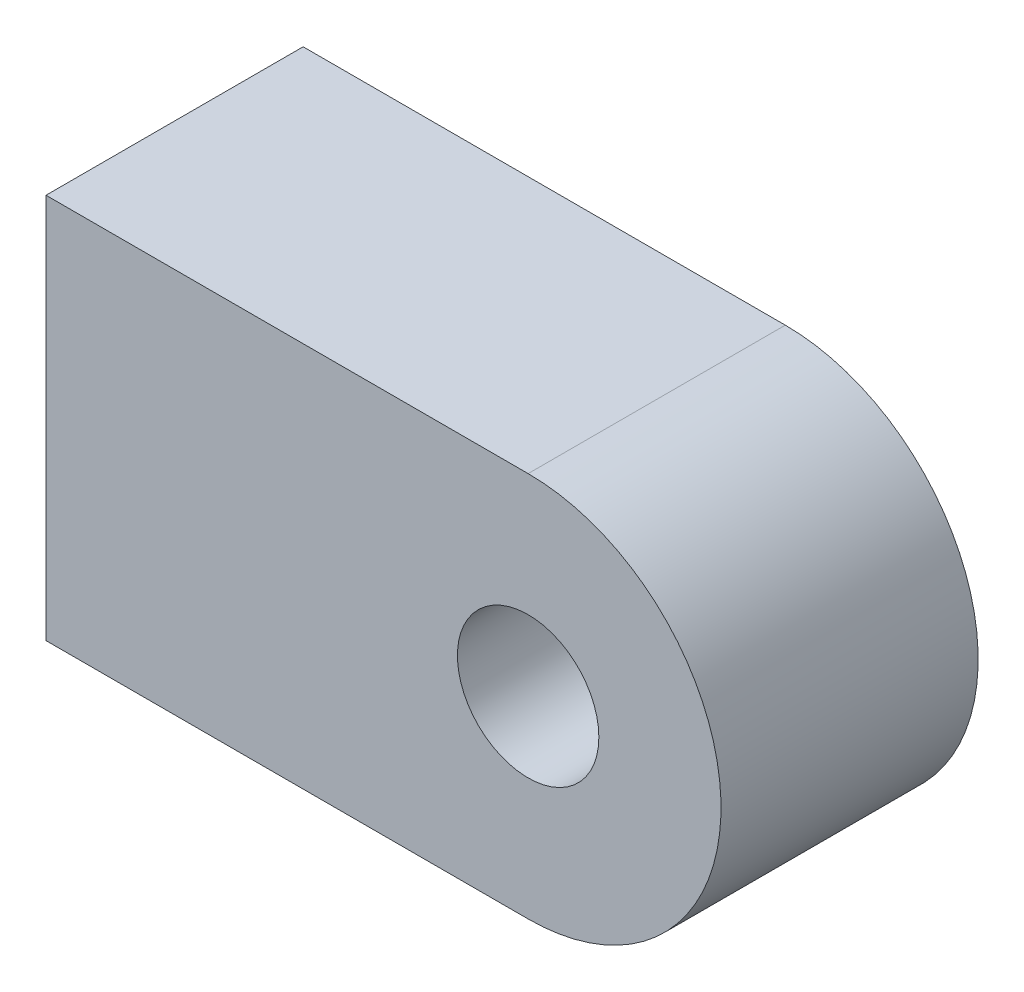
SolidWorks part; units mm, degrees
ref_plane "Ebene vorne" through (0, 0, 0) normal (0, 0, 1) x (1, 0, 0)
ref_plane "Ebene oben" through (0, 0, 0) normal (0, 1, 0) x (1, 0, 0)
ref_plane "Ebene rechts" through (0, 0, 0) normal (1, 0, 0) x (0, 0, -1)
sketch "Skizze1" plane through (0, 0, 0) normal (0, 0, 1) x (1, 0, 0)
  line L0 (0, -7.5) -> (-18.75, -7.5)
  line L1 (-18.75, -7.5) -> (-18.75, 7.5)
  line L2 (-18.75, 7.5) -> (0, 7.5)
  line L3 (-2.75, 0) -> (-18.75, 0) construction
  circle A0 centre (0, 0) radius 2.75
  arc A1 (0, 7.5) -> (0, -7.5) centre (0, 0) cw
  dimension "D1" = 5.5
  dimension "D2" = 16
  dimension "D3" = 15
extrude "Aufsatz-Linear austragen1" add sketch "Skizze1" along normal blind 10
